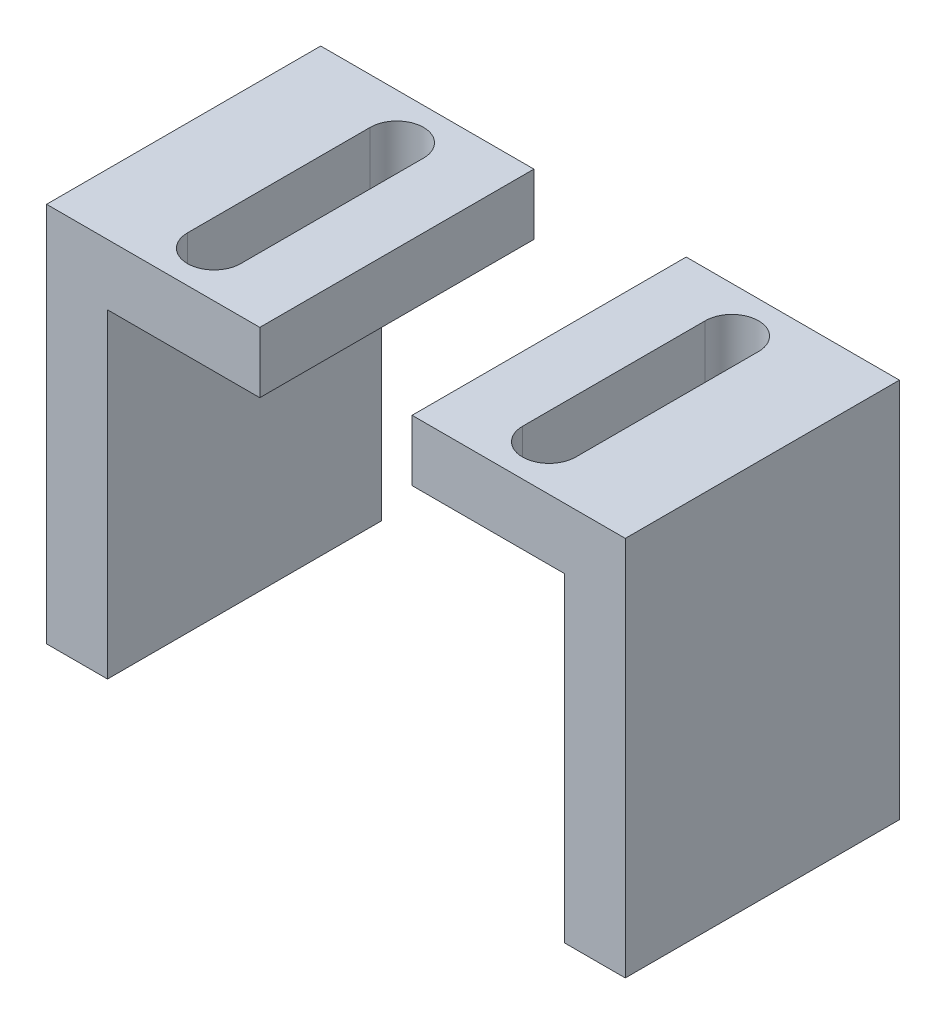
SolidWorks part; units mm, degrees
ref_plane "Front Plane" through (0, 0, 0) normal (0, 0, 1) x (1, 0, 0)
ref_plane "Top Plane" through (0, 0, 0) normal (0, 1, 0) x (1, 0, 0)
ref_plane "Right Plane" through (0, 0, 0) normal (1, 0, 0) x (0, 0, -1)
sketch "Sketch2" plane through (0, 0, 0) normal (0, 0, 1) x (1, 0, 0)
  line L0 (0, 0) -> (-10, 0)
  line L1 (-10, 0) -> (-10, -21)
  line L2 (-10, -21) -> (-14, -21)
  line L3 (-14, -21) -> (-14, 4)
  line L4 (-14, 4) -> (0, 4)
  line L5 (0, 4) -> (0, 0)
  line L6 (1, 25.9756) -> (1, -30.0687) construction
  dimension "D1" = 25
  dimension "D2" = 4
  dimension "D3" = 10
extrude "Boss-Extrude1" add sketch "Sketch2" along normal blind 18
sketch "Sketch3" plane through (0, 4, 0) normal (0, 1, 0) x (1, 0, 0)
  line L0 (-4.25, -3) -> (-4.25, -15)
  line L1 (0, -18) -> (0, 0) construction
  line L2 (-7.75, -3) -> (-7.75, -15)
  line L4 (0, 0) -> (-14, 0) construction
  arc A0 (-4.25, -3) -> (-7.75, -3) centre (-6, -3) ccw
  arc A1 (-7.75, -15) -> (-4.25, -15) centre (-6, -15) ccw
  dimension "D1" = 3.5
  dimension "D3" = 6
  dimension "D4" = 6
  dimension "D5" = 12
  dimension "D6" = 3
extrude "Cut-Extrude1" cut sketch "Sketch3" against normal blind 18
ref_plane "Plane1" through (5, 0, 0) normal (1, 0, 0) x (0, 0, -1)
mirror "Mirror2" about plane through (5, 0, 0) normal (1, 0, 0) of bodies 103
